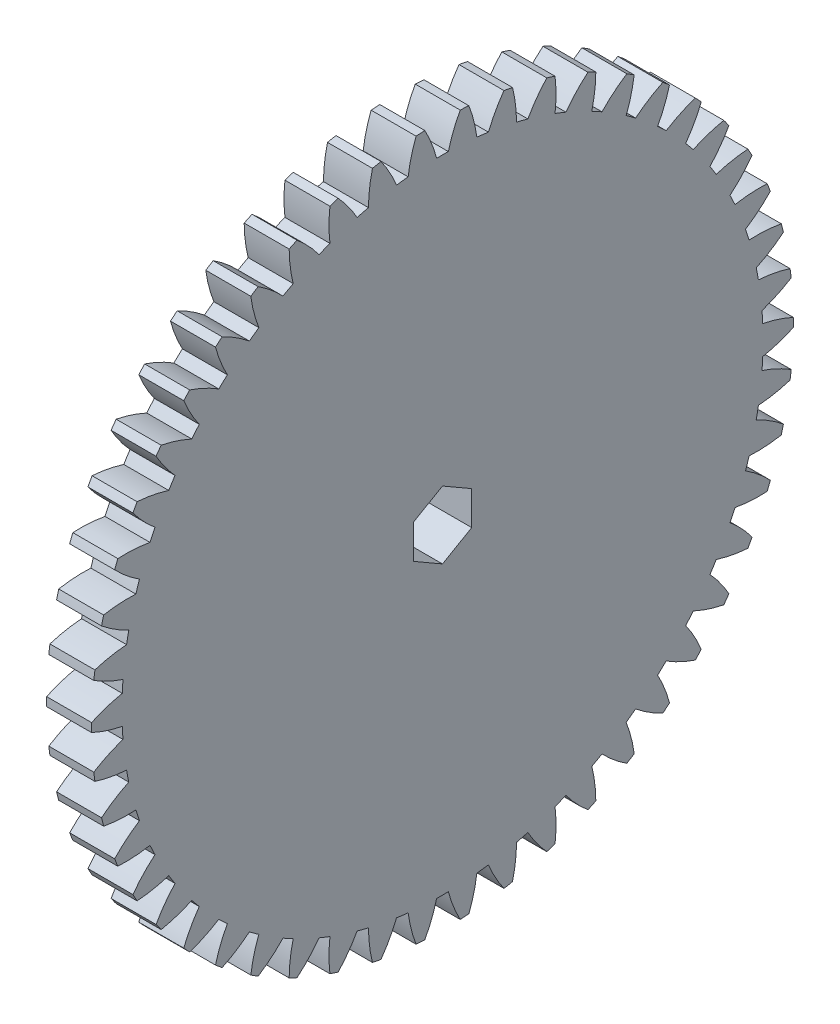
SolidWorks part; units mm, degrees
ref_plane "Plane1" through (0, 0, 0) normal (0, 0, 1) x (1, 0, 0)
ref_plane "Plane2" through (0, 0, 0) normal (0, 1, 0) x (1, 0, 0)
ref_plane "Plane3" through (0, 0, 0) normal (1, 0, 0) x (0, 0, -1)
sketch "HoldingSke" plane through (0, 0, 0) normal (0, 1, 0) x (1, 0, 0)
  line L0 (0, 0) -> (0.4285, -0.5107)
  line L1 (-15, 0) -> (100, 0) construction
  line L2 (0, 0) -> (-2.1039, 2.3779)
  line L3 (0, 0) -> (-11.863, 4.5341)
  line L4 (0, 0) -> (5.5511, 6.6156)
  line L5 (0, 0) -> (-46.8476, -17.4728)
  line L6 (0, 0) -> (-4.1448, -2.7965)
  line L7 (-2.1039, 2.3779) -> (8.6586, 51.2059)
  line L8 (-76.2, 54.61) -> (-75.3, 54.61)
  line L9 (-71.009, 38.7566) -> (-53.1078, 45.2721)
  line L10 (-76.2, 71.12) -> (104.1128, 71.12)
  line L11 (0, 0) -> (-5, 0)
  line L12 (-76.2, 101.6) -> (-76.147, 101.6)
  line L13 (24.9733, 27.94) -> (52.9518, 28.4284)
  line L14 (24.9733, 27.94) -> (24.9743, 27.94)
  line L15 (24.9733, 27.94) -> (100.4006, 29.5858)
  line L16 (-63.627, -1.5) -> (-12.827, -1.5)
  circle A0 centre (0, 0) radius 2.5
  circle A1 centre (0, 0) radius 35.624
  circle A2 centre (0, 0) radius 37.5
  circle A3 centre (0, 0) radius 2.5
  dimension "MHD" = 71.248
  dimension "Hub_dia" = 75
  dimension "Bore" = 5
  dimension "MBD" = 5
  dimension "Num_teeth" = 50
  dimension "Pitch" = 0.6667
  dimension "Overall_len" = 50
  dimension "Show_teeth" = 50
  dimension "Thickness" = 5
  dimension "OAL" = 50.0001
  dimension "T_dim" = 0.9
  dimension "Ap" = 20
  dimension "H" = 19.05
  dimension "Pitch_radius" = 180.3128
  dimension "Width" = 5
  dimension "Backlash" = 0.053
  dimension "Addendum_fac" = 1
  dimension "Dedendum_fac" = 1.25
  dimension "Clearance_fac" = 0.25
  dimension "Dedendum_add" = 0.001
  dimension "Module" = 1.5
sketch "BasProSke" plane through (0, 0, 0) normal (0, 1, 0) x (1, 0, 0)
  line L0 (-10, 0) -> (60, 0) construction
  line L1 (0, 0) -> (0, 39)
  line L2 (0, 0) -> (5, 0)
  line L3 (5, 0) -> (5, 39)
  line L4 (5, 39) -> (0, 39)
  dimension "Thickness" = 5
  dimension "Diameter" = 78
revolve "Base-Revolve" add sketch "BasProSke" angle 360 about L0
sketch "TooCutSke" plane through (0, 0, 0) normal (1, 0, 0) x (0, 0, -1)
  line L1 (0, 0) -> (0, 107) construction
  line L2 (0, 0) -> (-1.2706, 37.4785) construction
  line L3 (0, 0) -> (-4.7073, 74.8207) construction
  line L4 (-1.2706, 37.4785) -> (-2.3537, 37.4103) construction
  arc A0 (0.65, 35.6181) -> (-0.65, 35.6181) centre (0, 0) ccw
  arc A1 (1.9801, 38.9751) -> (-1.9801, 38.9751) centre (0, 0) ccw
  circle A2 centre (0, 0) radius 37.5 construction
  circle A3 centre (0, 0) radius 35.2385 construction
  arc A4 (-0.65, 35.6181) -> (-1.9801, 38.9751) centre (-15.1589, 31.8113) ccw
  arc A5 (1.9801, 38.9751) -> (0.65, 35.6181) centre (15.1589, 31.8113) ccw
  dimension "Root_dia" = 71.248
  dimension "Overcut_dia" = 78.0508
  dimension "Pitch_dia" = 75
  dimension "Base_dia" = 70.4769
  dimension "Flank_rad" = 15
  dimension "Half_ang" = 3.6
  dimension "Half_CT" = 1.0852
extrude "ToothCut" cut sketch "TooCutSke" along normal through all
fillet "Breaks" [suppressed] radius 0.03
fillet "RootFillets" [suppressed] radius 0.376
pattern_circular "TeethCuts" count 50 every 7.2 about axis through (-10, 0, 0) along (1, 0, 0) of "ToothCut", "RootFillets", "Breaks"
sketch "HubNeaOneSke" plane through (0, 0, 0) normal (-1, 0, 0) x (0, 0, 1)
  circle A0 centre (0, 0) radius 35.624
  dimension "Diameter" = 71.248
extrude "HubNearOne" [suppressed] add sketch "HubNeaOneSke" along normal blind 45.0001
sketch "HubNeaBotSke" plane through (0, 0, 0) normal (-1, 0, 0) x (0, 0, 1)
  circle A0 centre (0, 0) radius 35.624
  dimension "Diameter" = 71.248
extrude "HubNearBoth" [suppressed] add sketch "HubNeaBotSke" along normal blind 22.5
ref_plane "FarPln" through (5, 0, 0) normal (1, 0, 0) x (0, 0, -1)
sketch "HubFarSke" plane through (5, 0, 0) normal (1, 0, 0) x (0, 0, -1)
  circle A0 centre (0, 0) radius 35.624
  dimension "Diameter" = 71.248
extrude "HubFar" [suppressed] add sketch "HubFarSke" along normal blind 22.5
sketch "BorSke" plane through (0, 0, 0) normal (1, 0, 0) x (0, 0, -1)
  line L1 (0, -3.75) -> (3.2476, -1.875)
  line L2 (3.2476, -1.875) -> (3.2476, 1.875)
  line L3 (3.2476, 1.875) -> (0, 3.75)
  line L4 (0, 3.75) -> (-3.2476, 1.875)
  line L5 (-3.2476, 1.875) -> (-3.2476, -1.875)
  line L6 (-3.2476, -1.875) -> (0, -3.75)
  circle A0 centre (0, 0) radius 3.75 construction
  circle A1 centre (0, 0) radius 3.2476 construction
  dimension "Diameter" = 7.5
extrude "Bore" cut sketch "BorSke" along normal mid plane 100.0001
sketch "KeySke" plane through (0, 0, 0) normal (1, 0, 0) x (0, 0, -1)
  line L0 (-1, 0) -> (-1, 3.4)
  line L1 (-1, 3.4) -> (1, 3.4)
  line L2 (1, 3.4) -> (1, 0)
  line L3 (0, 0) -> (0, 34) construction
  line L4 (-1, 0) -> (1, 0)
  dimension "Offset" = 3.4
  dimension "Width" = 2
extrude "Keyway" [suppressed] cut sketch "KeySke" along normal mid plane 100.0001
pattern_circular "Keyway2" [suppressed] count 2 every 90 about axis through (-10, 0, 0) along (1, 0, 0)
sketch "Sketch1" plane through (0, 0, 0) normal (-1, 0, 0) x (0, 0, 1)
  line L12 (3.2476, -1.875) -> (3.2476, 1.875) construction
  line L13 (3.2476, 1.875) -> (0, 3.75) construction
  line L14 (0, 3.75) -> (-3.2476, 1.875) construction
  line L15 (-3.2476, 1.875) -> (-3.2476, -1.875) construction
  line L16 (-3.2476, -1.875) -> (0, -3.75) construction
  line L17 (0, -3.75) -> (3.2476, -1.875) construction
  line L18 (3.2476, -1.875) -> (3.2476, 1.875)
  line L19 (3.2476, 1.875) -> (0, 3.75)
  line L20 (0, 3.75) -> (-3.2476, 1.875)
  line L21 (-3.2476, 1.875) -> (-3.2476, -1.875)
  line L22 (-3.2476, -1.875) -> (0, -3.75)
  line L23 (0, -3.75) -> (3.2476, -1.875)
  line L24 (4.5499, -3.3057) -> (-4.5499, 3.3057) construction
  arc A40 (0.1868, -8.9981) -> (0.8757, -5.5554) centre (-1.8542, -6.7994) ccw
  arc A41 (-0.1868, -8.9981) -> (0.1868, -8.9981) centre (0, 0) ccw
  arc A42 (-0.8757, -5.5554) -> (-0.1868, -8.9981) centre (1.8542, -6.7994) ccw
  arc A43 (-2.5569, -5.0091) -> (-0.8757, -5.5554) centre (0, 0) ccw
  arc A44 (-5.1378, -7.3894) -> (-2.5569, -5.0091) centre (-5.4967, -4.4109) ccw
  arc A45 (-5.4401, -7.1698) -> (-5.1378, -7.3894) centre (0, 0) ccw
  arc A46 (-3.9738, -3.9797) -> (-5.4401, -7.1698) centre (-2.4965, -6.5907) ccw
  arc A47 (-5.0129, -2.5496) -> (-3.9738, -3.9797) centre (0, 0) ccw
  arc A48 (-8.4999, -2.9582) -> (-5.0129, -2.5496) centre (-7.0396, -0.3377) ccw
  arc A49 (-8.6154, -2.6029) -> (-8.4999, -2.9582) centre (0, 0) ccw
  arc A50 (-5.5541, -0.8839) -> (-8.6154, -2.6029) centre (-5.8936, -3.8646) ccw
  arc A51 (-5.5541, 0.8839) -> (-5.5541, -0.8839) centre (0, 0) ccw
  arc A52 (-8.6154, 2.6029) -> (-5.5541, 0.8839) centre (-5.8936, 3.8646) ccw
  arc A53 (-8.4999, 2.9582) -> (-8.6154, 2.6029) centre (0, 0) ccw
  arc A54 (-5.0129, 2.5496) -> (-8.4999, 2.9582) centre (-7.0396, 0.3377) ccw
  arc A55 (-3.9738, 3.9797) -> (-5.0129, 2.5496) centre (0, 0) ccw
  arc A56 (-5.4401, 7.1698) -> (-3.9738, 3.9797) centre (-2.4965, 6.5907) ccw
  arc A57 (-5.1378, 7.3894) -> (-5.4401, 7.1698) centre (0, 0) ccw
  arc A58 (-2.5569, 5.0091) -> (-5.1378, 7.3894) centre (-5.4967, 4.4109) ccw
  arc A59 (-0.8757, 5.5554) -> (-2.5569, 5.0091) centre (0, 0) ccw
  arc A60 (-0.1868, 8.9981) -> (-0.8757, 5.5554) centre (1.8542, 6.7994) ccw
  arc A61 (0.1868, 8.9981) -> (-0.1868, 8.9981) centre (0, 0) ccw
  arc A62 (0.8757, 5.5554) -> (0.1868, 8.9981) centre (-1.8542, 6.7994) ccw
  arc A63 (2.5569, 5.0091) -> (0.8757, 5.5554) centre (0, 0) ccw
  arc A64 (5.1378, 7.3894) -> (2.5569, 5.0091) centre (5.4967, 4.4109) ccw
  arc A65 (5.4401, 7.1698) -> (5.1378, 7.3894) centre (0, 0) ccw
  arc A66 (3.9738, 3.9797) -> (5.4401, 7.1698) centre (2.4965, 6.5907) ccw
  arc A67 (5.0129, 2.5496) -> (3.9738, 3.9797) centre (0, 0) ccw
  arc A68 (8.4999, 2.9582) -> (5.0129, 2.5496) centre (7.0396, 0.3377) ccw
  arc A69 (8.6154, 2.6029) -> (8.4999, 2.9582) centre (0, 0) ccw
  arc A70 (5.5541, 0.8839) -> (8.6154, 2.6029) centre (5.8936, 3.8646) ccw
  arc A71 (5.5541, -0.8839) -> (5.5541, 0.8839) centre (0, 0) ccw
  arc A72 (8.6154, -2.6029) -> (5.5541, -0.8839) centre (5.8936, -3.8646) ccw
  arc A73 (8.4999, -2.9582) -> (8.6154, -2.6029) centre (0, 0) ccw
  arc A74 (5.0129, -2.5496) -> (8.4999, -2.9582) centre (7.0396, -0.3377) ccw
  arc A75 (3.9738, -3.9797) -> (5.0129, -2.5496) centre (0, 0) ccw
  arc A76 (5.4401, -7.1698) -> (3.9738, -3.9797) centre (2.4965, -6.5907) ccw
  arc A77 (5.1378, -7.3894) -> (5.4401, -7.1698) centre (0, 0) ccw
  arc A78 (2.5569, -5.0091) -> (5.1378, -7.3894) centre (5.4967, -4.4109) ccw
  arc A79 (0.8757, -5.5554) -> (2.5569, -5.0091) centre (0, 0) ccw
extrude "Boss-Extrude1" add sketch "Sketch1" along normal blind 11.2
equation "' \"Module@HoldingSke\" = 6.35"
equation "' \"Num_teeth@HoldingSke\" = 12"
equation "' \"Ap@HoldingSke\" =  20"
equation "' \"Ap@HoldingSke\" = 20"
equation "' \"Width@HoldingSke\" = 0.5 * 25.4"
equation "' \"Hub_dia@HoldingSke\"= 1 * 25.4"
equation "' \"Hub_dia@HoldingSke\" = 1 * 25.4"
equation "' \"Overall_len@HoldingSke\" = 1.0 * 25.4"
equation "' \"Bore@HoldingSke\" = 0.75 * 25.4"
equation "' \"T_dim@HoldingSke\" = 0.1 * 25.4"
equation "' \"Width@KeySke\" = 0.25 * 25.4"
equation "' \"Show_teeth@HoldingSke\" = 13"
equation "' \"Backlash@HoldingSke\" = 0.009 * 25.4"
equation "' \"Addendum_fac@HoldingSke\" = 1.0"
equation "' \"Dedendum_fac@HoldingSke\" = 1.25"
equation "' \"Dedendum_add@HoldingSke\" = 0.00005 * 25.4"
equation "' \"Clearance_fac@HoldingSke\" = 0.25"
equation "\"Pitch@HoldingSke\" = 1 / \"Module@HoldingSke\""
equation "\"Overcut_dia@TooCutSke\" = (\"Num_teeth@HoldingSke\" + 2 * \"Addendum_fac@HoldingSke\") / \"Pitch@HoldingSke\" + 0.002 * 25.4"
equation "\"Pitch_dia@TooCutSke\" = \"Num_teeth@HoldingSke\" / \"Pitch@HoldingSke\""
equation "\"Base_dia@TooCutSke\" = \"Num_teeth@HoldingSke\" / \"Pitch@HoldingSke\" * cos((\"Ap@HoldingSke\"  * 3.14159265 / 180))"
equation "\"Root_dia@TooCutSke\" = (\"Num_teeth@HoldingSke\" + 2) / \"Pitch@HoldingSke\" - 2 * (\"Addendum_fac@HoldingSke\" + \"Dedendum_fac@HoldingSke\") / \"Pitch@HoldingSke\" - \"Dedendum_add@HoldingSke\" * 2"
equation "\"Half_ang@TooCutSke\" = 180 / \"Num_teeth@HoldingSke\""
equation "\"Half_CT@TooCutSke\" = \"Num_teeth@HoldingSke\" / \"Pitch@HoldingSke\" * sin((3.14159265 / 2 / \"Num_teeth@HoldingSke\")) / 2 - 7 * \"Backlash@HoldingSke\" / 4"
equation "\"Flank_rad@TooCutSke\" = \"Num_teeth@HoldingSke\" / \"Pitch@HoldingSke\" / 5"
equation "\"Radius@RootFillets\" = \"Clearance_fac@HoldingSke\" / \"Pitch@HoldingSke\" + \"Dedendum_add@HoldingSke\""
equation "\"Break_rad@Breaks\" = 0.02 / \"Pitch@HoldingSke\""
equation "\"Thickness@HoldingSke\" = \"Width@HoldingSke\""
equation "\"OAL@HoldingSke\" = \"Thickness@HoldingSke\""
equation "\"MHD@HoldingSke\" = (\"Num_teeth@HoldingSke\" + 2) / \"Pitch@HoldingSke\" - 2 * (\"Addendum_fac@HoldingSke\" + \"Dedendum_fac@HoldingSke\")  / \"Pitch@HoldingSke\" - \"Dedendum_add@HoldingSke\" * 2"
equation "\"MBD@HoldingSke\" = (\"Num_teeth@HoldingSke\" + 2) / \"Pitch@HoldingSke\" - 2 * (\"Addendum_fac@HoldingSke\" + \"Dedendum_fac@HoldingSke\")  / \"Pitch@HoldingSke\" - \"Dedendum_add@HoldingSke\" * 2 - 0.002 * 25.4"
equation "\"MHD@HoldingSke\" = ((sgn( \"MHD@HoldingSke\" - \"Hub_dia@HoldingSke\" )-1)*( \"MHD@HoldingSke\" - \"Hub_dia@HoldingSke\" ))/-2+ \"Hub_dia@HoldingSke\""
equation "\"MBD@HoldingSke\" = ((sgn( \"MBD@HoldingSke\" - \"Bore@HoldingSke\" )-1)*( \"MBD@HoldingSke\" - \"Bore@HoldingSke\" ))/-2+ \"Bore@HoldingSke\""
equation "\"OAL@HoldingSke\" = ((sgn( \"OAL@HoldingSke\" - \"Overall_len@HoldingSke\" )+1)*( \"OAL@HoldingSke\" - \"Overall_len@HoldingSke\" ))/2 + \"Overall_len@HoldingSke\" + 0.000002 * 25.4"
equation "\"Num_teeth@TeethCuts\" = int( \"Show_teeth@HoldingSke\" ) + 1"
equation "\"Num_teeth@TeethCuts\" = ((sgn( \"Num_teeth@TeethCuts\" - \"Num_teeth@HoldingSke\" )-1)*( \"Num_teeth@TeethCuts\" - \"Num_teeth@HoldingSke\" ))/-2+ \"Num_teeth@HoldingSke\""
equation "\"Num_teeth@TeethCuts\" = ((sgn( \"Num_teeth@TeethCuts\" - 2.0)+1)*( \"Num_teeth@TeethCuts\" - 2.0))/2 +2.0"
equation "\"Angle@TeethCuts\" = 360.0 / \"Num_teeth@HoldingSke\""
equation "\"Diameter@BasProSke\" = (\"Num_teeth@HoldingSke\" + 2 * \"Addendum_fac@HoldingSke\") / \"Pitch@HoldingSke\""
equation "\"Thickness@BasProSke\"  = \"Thickness@HoldingSke\""
equation "' \"Fillet_rad@BasProSke\" =  \"Thickness@HoldingSke\" * 0.05"
equation "' \"Fillet_rad@BasProSke\" = \"Thickness@HoldingSke\" * 0.05"
equation "\"MHD@HoldingSke\" = ((sgn( \"MHD@HoldingSke\" - \"Root_dia@TooCutSke\" )-1)*( \"MHD@HoldingSke\" - \"Root_dia@TooCutSke\" ))/-2+ \"Root_dia@TooCutSke\""
equation "\"Diameter@HubNeaOneSke\" = \"MHD@HoldingSke\""
equation "\"Length@HubNearOne\" = \"OAL@HoldingSke\" - \"Thickness@BasProSke\""
equation "\"Diameter@HubNeaBotSke\" = \"MHD@HoldingSke\""
equation "\"Length@HubNearBoth\" = ( \"OAL@HoldingSke\" - \"Thickness@BasProSke\" ) / 2.0"
equation "\"Thickness@FarPln\" = \"Thickness@BasProSke\""
equation "\"Diameter@HubFarSke\" = \"MHD@HoldingSke\""
equation "\"Length@HubFar\" = ( \"OAL@HoldingSke\" - \"Thickness@BasProSke\" ) / 2.0"
equation "\"Diameter@BorSke\"=7.5"
equation "\"D1@Bore\" = \"OAL@HoldingSke\" * 2.0"
equation "\"D1@Keyway\" = \"OAL@HoldingSke\" * 2.0"
equation "\"Offset@KeySke\" = \"T_dim@HoldingSke\" + \"MBD@HoldingSke\" / 2.0"
